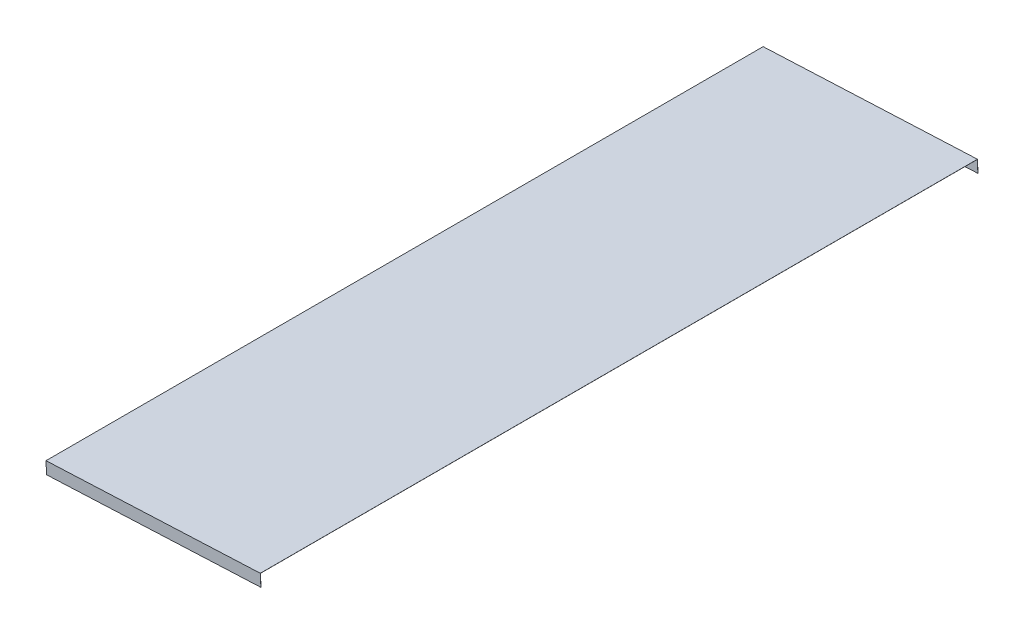
SolidWorks part; units mm, degrees
ref_plane "Front Plane" through (0, 0, 0) normal (0, 0, 1) x (1, 0, 0)
ref_plane "Top Plane" through (0, 0, 0) normal (0, 1, 0) x (1, 0, 0)
ref_plane "Right Plane" through (0, 0, 0) normal (1, 0, 0) x (0, 0, -1)
sketch "Sketch1" plane through (0, 0, 0) normal (0, 0, 1) x (1, 0, 0)
  line L0 (-169.0031, 11.7142) -> (-694.187, 895.1707) construction
  line L1 (-1723.9711, 565.2543) -> (-1544.6455, 573.3415)
  line L2 (-1723.9756, 565.3542) -> (-1723.9711, 565.2543)
  line L3 (-1723.9756, 565.3542) -> (-1544.65, 573.4414)
  line L4 (-1544.65, 573.4414) -> (-1544.6455, 573.3415)
  dimension "D1" = 0.1
extrude "Boss-Extrude2" add sketch "Sketch1" along normal blind 600
sketch "Sketch2" plane through (-28.9438, 641.7968, 0) normal (-0.0451, 0.999, 0) x (0.999, 0.0451, 0)
  line L0 (-1696.7546, 0) -> (-1696.7546, -0.1)
  line L1 (-1696.7546, -600) -> (-1696.7546, 0) construction
  line L2 (-1696.7546, -0.1) -> (-1517.2467, -0.1)
  line L3 (-1517.2467, -600) -> (-1517.2467, 0) construction
  line L4 (-1517.2467, -0.1) -> (-1517.2467, 0)
  line L5 (-1517.2467, 0) -> (-1696.7546, 0)
extrude "Boss-Extrude3" add sketch "Sketch2" against normal blind 10
sketch "Sketch3" plane through (-28.9438, 641.7968, 0) normal (-0.0451, 0.999, 0) x (0.999, 0.0451, 0)
  line L0 (-1696.7546, -600) -> (-1696.7546, -599.9)
  line L1 (-1696.7546, -600) -> (-1696.7546, 0) construction
  line L2 (-1696.7546, -599.9) -> (-1517.2467, -599.9)
  line L3 (-1517.2467, -600) -> (-1517.2467, 0) construction
  line L4 (-1517.2467, -599.9) -> (-1517.2467, -600)
  line L5 (-1517.2467, -600) -> (-1696.7546, -600)
extrude "Boss-Extrude4" add sketch "Sketch3" against normal blind 10
